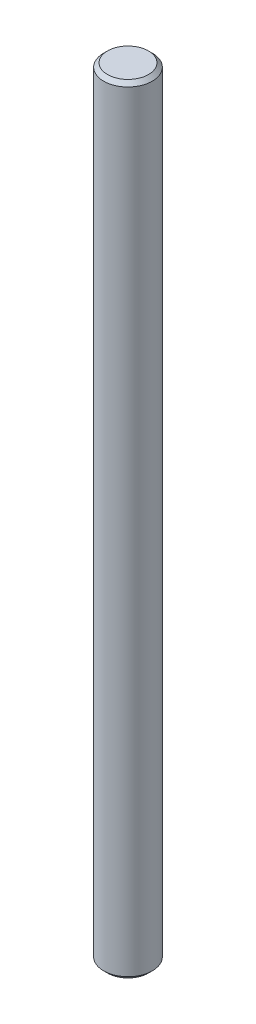
SolidWorks part; units mm, degrees
ref_plane "Front Plane" through (0, 0, 0) normal (0, 0, 1) x (1, 0, 0)
ref_plane "Top Plane" through (0, 0, 0) normal (0, 1, 0) x (1, 0, 0)
ref_plane "Right Plane" through (0, 0, 0) normal (1, 0, 0) x (0, 0, -1)
sketch "Bar face" plane through (0, 0, 0) normal (0, 1, 0) x (1, 0, 0)
  circle A0 centre (0, 0) radius 3.175
  dimension "D1" = 6.35
extrude "Bar extrude" add sketch "Bar face" along normal blind 101.6
chamfer "Chamfer2" distance 0.5 2 edges at (0, 101.6, 3.175) (0, 0, 3.175)
